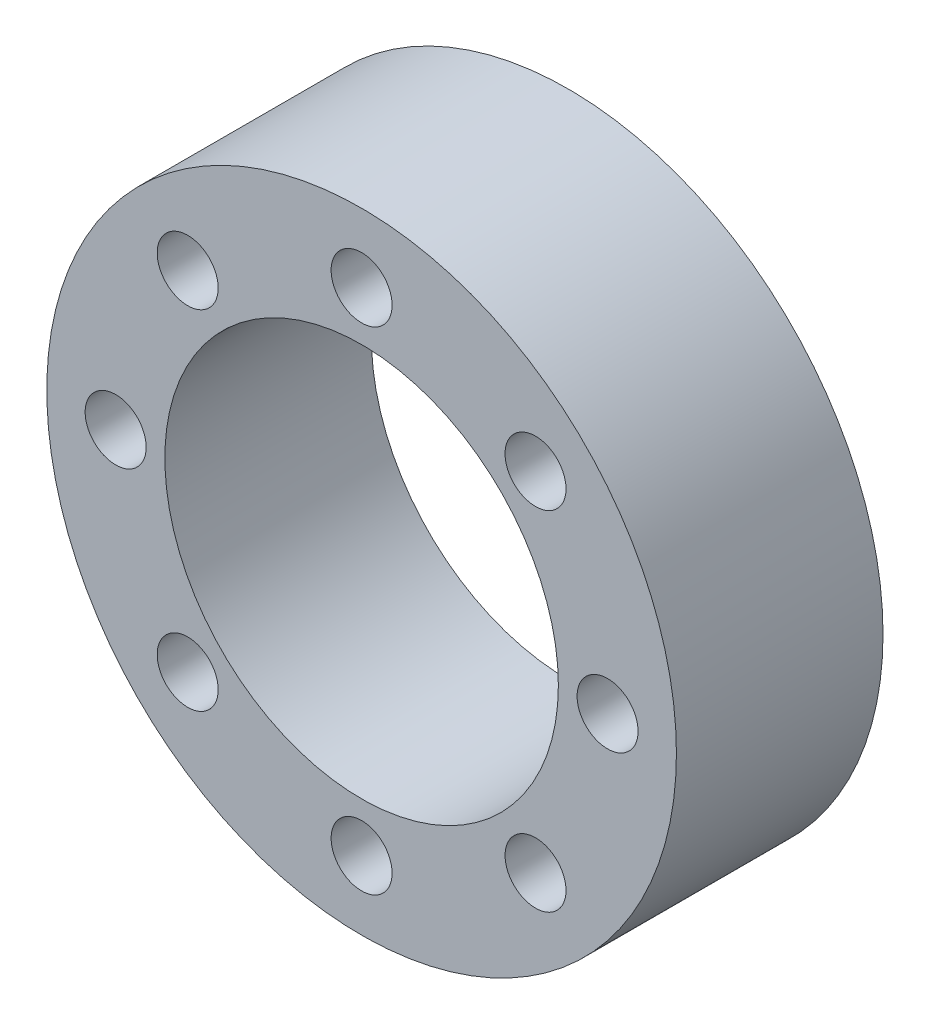
SolidWorks part; units mm, degrees
material "Thornel Mat VMA"
ref_plane "前视基准面" through (0, 0, 0) normal (0, 0, 1) x (1, 0, 0)
ref_plane "上视基准面" through (0, 0, 0) normal (0, 1, 0) x (1, 0, 0)
ref_plane "右视基准面" through (0, 0, 0) normal (1, 0, 0) x (0, 0, -1)
sketch "草图1" plane through (0, 0, 0) normal (0, 0, 1) x (1, 0, 0)
  circle A0 centre (0, 0) radius 16
  circle A1 centre (0, 0) radius 12.5 construction
  circle A2 centre (0, 12.5) radius 1.55
  circle A3 centre (8.8388, 8.8388) radius 1.55
  circle A4 centre (12.5, 0) radius 1.55
  circle A5 centre (8.8388, -8.8388) radius 1.55
  circle A6 centre (0, -12.5) radius 1.55
  circle A7 centre (-8.8388, -8.8388) radius 1.55
  circle A8 centre (-12.5, 0) radius 1.55
  circle A9 centre (-8.8388, 8.8388) radius 1.55
  circle A10 centre (0, 0) radius 10
  dimension "D1" = 32
  dimension "D2" = 25
  dimension "D4" = 3.1
  dimension "D5" = 20
  dimension "D3" = 8
extrude "凸台-拉伸1" add sketch "草图1" along normal blind 10.5
